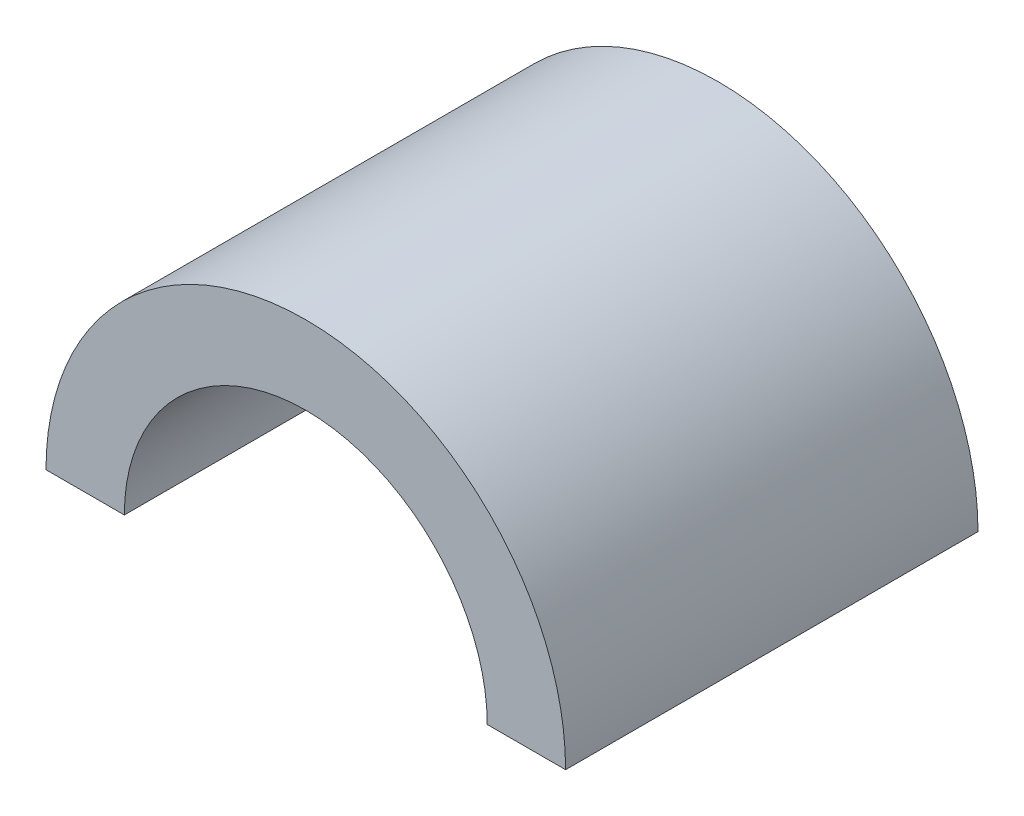
SolidWorks part; units mm, degrees
material "Natural Rubber"
ref_plane "Front Plane" through (0, 0, 0) normal (0, 0, 1) x (1, 0, 0)
ref_plane "Top Plane" through (0, 0, 0) normal (0, 1, 0) x (1, 0, 0)
ref_plane "Right Plane" through (0, 0, 0) normal (1, 0, 0) x (0, 0, -1)
sketch "Sketch1" plane through (0, 0, 0) normal (0, 0, 1) x (1, 0, 0)
  line L0 (-16.002, 0) -> (-11.176, 0)
  line L1 (11.176, 0) -> (16.002, 0)
  line L2 (-11.176, 0) -> (11.176, 0) construction
  arc A0 (11.176, 0) -> (-11.176, 0) centre (0, 0) ccw
  arc A1 (16.002, 0) -> (-16.002, 0) centre (0, 0) ccw
  dimension "D2" = 22.352
  dimension "D1" = 4.826
extrude "Boss-Extrude1" add sketch "Sketch1" along normal blind 25.4
